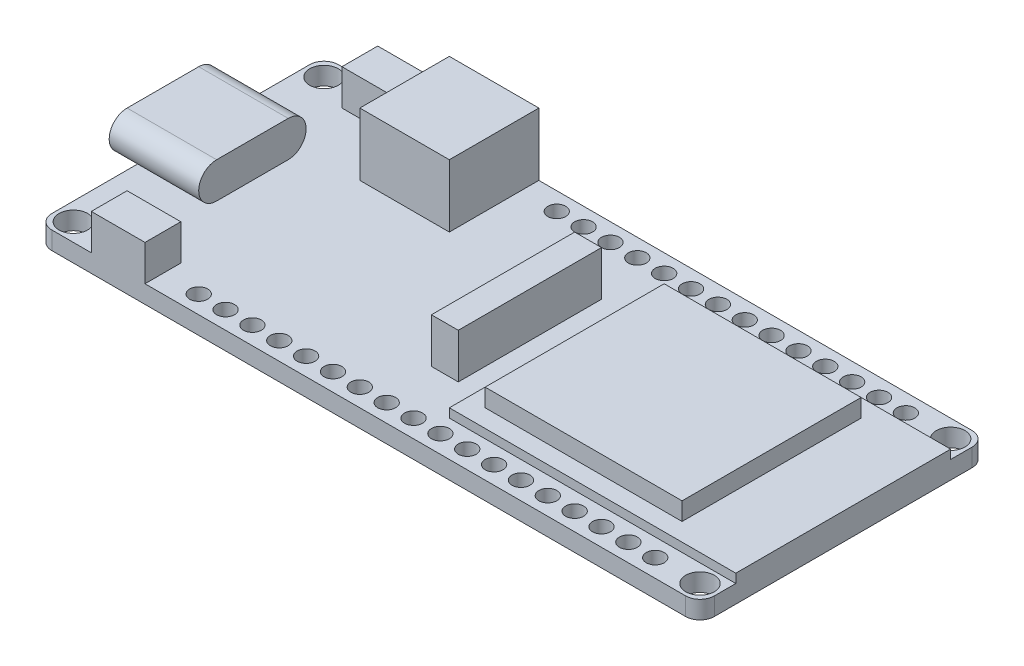
SolidWorks part; units mm, degrees
ref_plane "Front Plane" through (0, 0, 0) normal (0, 0, 1) x (1, 0, 0)
ref_plane "Top Plane" through (0, 0, 0) normal (0, 1, 0) x (1, 0, 0)
ref_plane "Right Plane" through (0, 0, 0) normal (1, 0, 0) x (0, 0, -1)
sketch "Sketch1" plane through (0, 0, 0) normal (0, 1, 0) x (1, 0, 0)
  line L1 (0, 0) -> (60.325, 0)
  line L2 (0, 0) -> (0, 25.4)
  line L3 (0, 25.4) -> (60.325, 25.4)
  line L4 (60.325, 0) -> (60.325, 25.4)
  line L5 (0, 25.4) -> (1.5875, 25.4)
  line L6 (0, 25.4) -> (0, 17.4625)
  line L7 (0, 17.4625) -> (1.5875, 17.4625)
  line L8 (1.5875, 25.4) -> (1.5875, 17.4625)
  line L9 (0, 0) -> (1.5875, 0)
  line L10 (0, 0) -> (0, 7.9375)
  line L11 (0, 7.9375) -> (1.5875, 7.9375)
  line L12 (1.5875, 0) -> (1.5875, 7.9375)
  dimension "D1" = 60.325
  dimension "D2" = 25.4
  dimension "D3" = 7.9375
  dimension "D4" = 1.5875
  dimension "D5" = 1.5875
  dimension "D6" = 7.9375
extrude "Boss-Extrude1" add sketch "Sketch1" along normal blind 1.5875 contours L12 L1 L4 L3 L8 L7 L2 L11
sketch "Sketch2" plane through (0, 1.5875, 0) normal (0, 1, 0) x (1, 0, 0)
  line L1 (0, 17.4625) -> (7.9375, 17.4625)
  line L2 (0, 17.4625) -> (0, 7.9375)
  line L3 (0, 7.9375) -> (7.9375, 7.9375)
  line L4 (7.9375, 17.4625) -> (7.9375, 7.9375)
  dimension "D1" = 9.525
  dimension "D2" = 7.9375
extrude "Boss-Extrude2" add sketch "Sketch2" along normal blind 3.175
sketch "Sketch3" plane through (0, 0, 0) normal (-1, 0, 0) x (0, 0, 1)
  line L0 (-7.9375, 4.7625) -> (-7.9375, 0) construction
  line L1 (-17.4625, 4.7625) -> (-7.9375, 4.7625)
  line L2 (-17.4625, 4.7625) -> (-17.4625, 1.5875)
  line L3 (-17.4625, 1.5875) -> (-7.9375, 1.5875)
  line L4 (-7.9375, 4.7625) -> (-7.9375, 1.5875)
  line L5 (-15.875, 3.175) -> (-9.525, 3.175) construction
  line L6 (-15.875, 4.7625) -> (-9.525, 4.7625)
  line L7 (-15.875, 1.5875) -> (-9.525, 1.5875)
  line L8 (-15.875, 3.175) -> (-9.525, 3.175) construction
  line L9 (-15.875, 3.5719) -> (-9.525, 3.5719)
  line L10 (-15.875, 3.5719) -> (-15.875, 2.7781)
  line L11 (-15.875, 2.7781) -> (-9.525, 2.7781)
  line L12 (-9.525, 3.5719) -> (-9.525, 2.7781)
  line L13 (-15.875, 4.3656) -> (-9.525, 4.3656)
  line L14 (-15.875, 1.9844) -> (-9.525, 1.9844)
  arc A0 (-15.875, 4.7625) -> (-15.875, 1.5875) centre (-15.875, 3.175) ccw
  arc A1 (-9.525, 1.5875) -> (-9.525, 4.7625) centre (-9.525, 3.175) ccw
  arc A2 (-15.875, 4.3656) -> (-15.875, 1.9844) centre (-15.875, 3.175) ccw
  arc A3 (-9.525, 1.9844) -> (-9.525, 4.3656) centre (-9.525, 3.175) ccw
  point P9 (-12.7, 3.175)
  point P16 (-12.7, 3.175)
  point P17 (-17.4625, 3.175)
  point P18 (-7.9375, 3.175)
  line M11 (-7.9375, 0) -> (-7.9375, 4.7625)
  line M12 (-7.9375, 4.7625) -> (-17.4625, 4.7625)
  line M13 (-17.4625, 4.7625) -> (-17.4625, 0)
  dimension "D1" = 3.175
  dimension "D2" = 0.7937
  dimension "D3" = 6.35
  dimension "D4" = 0.3969
  dimension "D5" = 3.175
  dimension "D6" = 0.3969
extrude "Cut-Extrude2" cut sketch "Sketch3" against normal blind 7.9375 contours A0 M12 M13 | A0 L2 L3 | A1 L4 M12 | A1 L3 M11
sketch "Sketch4" plane through (0, 0, 0) normal (-1, 0, 0) x (0, 0, 1)
  line L0 (-15.875, 3.175) -> (-9.525, 3.175) construction
  line L1 (-15.875, 4.3656) -> (-9.525, 4.3656)
  line L2 (-15.875, 1.9844) -> (-9.525, 1.9844)
  line L4 (-15.875, 1.5875) -> (-9.525, 1.5875)
  line L5 (-15.875, 4.7625) -> (-9.525, 4.7625) construction
  line L6 (-15.875, 3.5719) -> (-9.525, 3.5719)
  line L7 (-15.875, 3.5719) -> (-15.875, 2.7781)
  line L8 (-15.875, 2.7781) -> (-9.525, 2.7781)
  line L9 (-9.525, 3.5719) -> (-9.525, 2.7781)
  arc A0 (-15.875, 4.3656) -> (-15.875, 1.9844) centre (-15.875, 3.175) ccw
  arc A1 (-9.525, 1.9844) -> (-9.525, 4.3656) centre (-9.525, 3.175) ccw
  arc A3 (-15.875, 4.7625) -> (-15.875, 1.5875) centre (-15.875, 3.175) ccw construction
  arc A4 (-9.525, 1.5875) -> (-9.525, 4.7625) centre (-9.525, 3.175) ccw construction
  point P2 (-12.7, 3.175)
  dimension "D3" = 6.35
  dimension "D1" = 0.3969
  dimension "D2" = 0.3969
  dimension "D4" = 0.7937
  dimension "D5" = 3.175
extrude "Cut-Extrude3" cut sketch "Sketch4" against normal blind 5.3975 contours L2 A1 L1 A0 L6 L9 L8 L7
sketch "Sketch5" plane through (0, 0, 0) normal (0, -1, 0) x (1, 0, 0)
  line L1 (0, -17.4625) -> (1.5875, -17.4625)
  line L2 (0, -17.4625) -> (0, -7.9375)
  line L3 (0, -7.9375) -> (1.5875, -7.9375)
  line L4 (1.5875, -17.4625) -> (1.5875, -7.9375)
extrude "Cut-Extrude4" cut sketch "Sketch5" against normal blind 1.5875
sketch "Sketch6" plane through (0, 1.5875, 0) normal (0, 1, 0) x (1, 0, 0)
  line L0 (1.5875, 25.4) -> (60.325, 25.4) construction
  line L1 (1.5875, 25.4) -> (1.5875, 15.875) construction
  line L2 (60.325, 0) -> (60.325, 25.4) construction
  line L3 (1.5875, 0) -> (60.325, 0) construction
  line L9 (2.8575, 25.4) -> (59.055, 25.4)
  line L10 (1.5875, 24.13) -> (1.5875, 1.27)
  line L11 (2.8575, 0) -> (59.055, 0)
  line L12 (60.325, 24.13) -> (60.325, 1.27)
  line L13 (1.5875, 25.4) -> (60.325, 25.4)
  line L14 (1.5875, 25.4) -> (1.5875, 0)
  line L15 (1.5875, 0) -> (60.325, 0)
  line L16 (60.325, 25.4) -> (60.325, 0)
  circle A0 centre (3.175, 23.8125) radius 1.27
  circle A1 centre (3.175, 1.5875) radius 1.27
  circle A2 centre (58.7375, 1.5875) radius 1.27
  circle A3 centre (58.7375, 23.8125) radius 1.27
  arc A4 (59.055, 25.4) -> (60.325, 24.13) centre (59.055, 24.13) cw
  arc A5 (59.055, 0) -> (60.325, 1.27) centre (59.055, 1.27) ccw
  arc A6 (2.8575, 0) -> (1.5875, 1.27) centre (2.8575, 1.27) cw
  arc A7 (1.5875, 24.13) -> (2.8575, 25.4) centre (2.8575, 24.13) cw
  point P27 (60.325, 0)
  point P32 (1.5875, 25.4)
  line M18 (1.5875, 9.525) -> (1.5875, 0)
  line M19 (1.5875, 0) -> (60.325, 0)
  line M20 (60.325, 0) -> (60.325, 25.4)
  line M21 (60.325, 25.4) -> (1.5875, 25.4)
  line M22 (1.5875, 25.4) -> (1.5875, 15.875)
  dimension "D6" = 1.27
  dimension "D2" = 1.5875
  dimension "D3" = 1.5875
  dimension "D4" = 1.5875
  dimension "D5" = 1.5875
extrude "Cut-Extrude5" cut sketch "Sketch6" against normal blind 1.5875 contours A7 M22 M21 | A6 M19 M18 | A5 M19 M20 | A4 M21 M20 | A0 | A1 | A2 | A3
sketch "Sketch7" plane through (0, 1.5875, 0) normal (0, 1, 0) x (1, 0, 0)
  line L0 (2.8575, 25.4) -> (59.055, 25.4) construction
  line L1 (6.35, 25.4) -> (11.1125, 25.4)
  line L2 (6.35, 25.4) -> (6.35, 22.225)
  line L3 (6.35, 22.225) -> (11.1125, 22.225)
  line L4 (11.1125, 25.4) -> (11.1125, 22.225)
  line L5 (1.5875, 24.13) -> (1.5875, 15.875) construction
  line L6 (12.7, 25.4) -> (20.6375, 25.4)
  line L7 (12.7, 25.4) -> (12.7, 17.4625)
  line L8 (12.7, 17.4625) -> (20.6375, 17.4625)
  line L9 (20.6375, 25.4) -> (20.6375, 17.4625)
  line L10 (60.325, 1.27) -> (60.325, 24.13) construction
  line L11 (60.325, 22.225) -> (34.925, 22.225)
  line L12 (60.325, 22.225) -> (60.325, 3.175)
  line L13 (60.325, 3.175) -> (34.925, 3.175)
  line L14 (34.925, 22.225) -> (34.925, 3.175)
  line L15 (2.8575, 0) -> (59.055, 0) construction
  line L17 (36.5125, 20.6375) -> (54.1337, 20.6375)
  line L18 (36.5125, 20.6375) -> (36.5125, 4.7625)
  line L19 (36.5125, 4.7625) -> (54.1337, 4.7625)
  line L20 (54.1337, 20.6375) -> (54.1337, 4.7625)
  line L21 (30.1625, 19.05) -> (32.5437, 19.05)
  line L22 (30.1625, 19.05) -> (30.1625, 6.35)
  line L23 (30.1625, 6.35) -> (32.5437, 6.35)
  line L24 (32.5437, 19.05) -> (32.5437, 6.35)
  line L25 (6.35, 0) -> (11.1125, 0)
  line L26 (6.35, 0) -> (6.35, 3.175)
  line L27 (6.35, 3.175) -> (11.1125, 3.175)
  line L28 (11.1125, 0) -> (11.1125, 3.175)
  line M32 (60.325, 1.27) -> (60.325, 24.13)
  line M34 (59.055, 25.4) -> (2.8575, 25.4)
  dimension "D1" = 1.5875
  dimension "D2" = 7.9375
  dimension "D3" = 7.9375
  dimension "D4" = 4.7625
  dimension "D5" = 3.175
  dimension "D6" = 4.7625
  dimension "D7" = 3.175
  dimension "D8" = 3.175
  dimension "D9" = 25.4
  dimension "D10" = 1.5875
  dimension "D11" = 1.5875
  dimension "D12" = 1.5875
  dimension "D13" = 17.6212
  dimension "D14" = 2.3813
  dimension "D15" = 2.3813
  dimension "D16" = 6.35
  dimension "D17" = 6.35
extrude "Boss-Extrude3" add sketch "Sketch7" along normal blind 3.175 contours L20 L17 L18 L19 | L11 L14 L13 L17 L20 L19 L18 M32 | L4 L2 L3 M34 | L26 L25 L28 L27 | L7 L6 L9 L8 | L22 L21 L24 L23
sketch "Sketch10" plane through (0, 4.7625, 0) normal (0, 1, 0) x (1, 0, 0)
  line L0 (12.7, 17.4625) -> (20.6375, 17.4625) construction
  line L1 (12.7, 25.4) -> (20.6375, 25.4)
  line L2 (12.7, 25.4) -> (12.7, 17.4625)
  line L3 (12.7, 17.4625) -> (20.6375, 17.4625)
  line L4 (20.6375, 25.4) -> (20.6375, 17.4625)
extrude "Boss-Extrude4" add sketch "Sketch10" along normal blind 2.3813
sketch "Sketch11" plane through (0, 4.7625, 0) normal (0, 1, 0) x (1, 0, 0)
  line L1 (30.1625, 19.05) -> (32.5437, 19.05)
  line L2 (30.1625, 19.05) -> (30.1625, 6.35)
  line L3 (30.1625, 6.35) -> (32.5437, 6.35)
  line L4 (32.5437, 19.05) -> (32.5437, 6.35)
extrude "Boss-Extrude5" add sketch "Sketch11" along normal blind 0.7937
sketch "Sketch12" plane through (0, 4.7625, 0) normal (0, 1, 0) x (1, 0, 0)
  line L1 (34.925, 22.225) -> (60.325, 22.225)
  line L2 (34.925, 22.225) -> (34.925, 3.175)
  line L3 (34.925, 3.175) -> (60.325, 3.175)
  line L4 (60.325, 22.225) -> (60.325, 3.175)
extrude "Cut-Extrude6" cut sketch "Sketch12" against normal blind 0.7937
sketch "Sketch13" plane through (0, 3.9687, 0) normal (0, 1, 0) x (1, 0, 0)
  line L1 (34.925, 22.225) -> (60.325, 22.225)
  line L2 (34.925, 22.225) -> (34.925, 3.175)
  line L3 (34.925, 3.175) -> (60.325, 3.175)
  line L4 (60.325, 22.225) -> (60.325, 3.175)
  line L5 (36.5125, 20.6375) -> (53.975, 20.6375)
  line L6 (36.5125, 20.6375) -> (36.5125, 4.7625)
  line L7 (36.5125, 4.7625) -> (53.975, 4.7625)
  line L8 (53.975, 20.6375) -> (53.975, 4.7625)
  dimension "D1" = 1.5875
  dimension "D2" = 1.5875
  dimension "D3" = 1.5875
  dimension "D4" = 6.35
extrude "Cut-Extrude7" cut sketch "Sketch13" against normal blind 1.5875 contours L6 L5 L8 L7 | L2 L1 L4 L3
sketch "Sketch14" plane through (0, 1.5875, 0) normal (0, 1, 0) x (1, 0, 0)
  line L1 (60.325, 1.27) -> (60.325, 3.175) construction
  line L2 (60.325, 22.225) -> (60.325, 24.13) construction
  line L3 (20.6375, 25.4) -> (59.055, 25.4) construction
  line L4 (11.1125, 0) -> (59.055, 0) construction
  circle A0 centre (23.8125, 23.8125) radius 0.7937
  circle A1 centre (26.1937, 23.8125) radius 0.7937
  circle A2 centre (28.575, 23.8125) radius 0.7937
  circle A3 centre (30.9562, 23.8125) radius 0.7937
  circle A5 centre (38.1, 23.8125) radius 0.7937
  circle A6 centre (42.8625, 23.8125) radius 0.7937
  circle A7 centre (33.3375, 23.8125) radius 0.7937
  circle A8 centre (35.7187, 23.8125) radius 0.7937
  circle A9 centre (40.4812, 23.8125) radius 0.7937
  circle A10 centre (45.2437, 23.8125) radius 0.7937
  circle A11 centre (47.625, 23.8125) radius 0.7937
  circle A12 centre (50.0062, 23.8125) radius 0.7937
  circle A13 centre (52.3875, 23.8125) radius 0.7937
  circle A14 centre (54.7687, 23.8125) radius 0.7937
  circle A15 centre (14.2875, 1.5875) radius 0.7937
  circle A16 centre (16.6687, 1.5875) radius 0.7937
  circle A17 centre (19.05, 1.5875) radius 0.7937
  circle A18 centre (21.4312, 1.5875) radius 0.7937
  circle A19 centre (23.8125, 1.5875) radius 0.7937
  circle A20 centre (26.1937, 1.5875) radius 0.7937
  circle A21 centre (28.575, 1.5875) radius 0.7937
  circle A22 centre (30.9562, 1.5875) radius 0.7937
  circle A23 centre (33.3375, 1.5875) radius 0.7937
  circle A24 centre (35.7187, 1.5875) radius 0.7937
  circle A25 centre (38.1, 1.5875) radius 0.7937
  circle A26 centre (40.4812, 1.5875) radius 0.7937
  circle A27 centre (42.8625, 1.5875) radius 0.7937
  circle A28 centre (45.2437, 1.5875) radius 0.7937
  circle A29 centre (47.625, 1.5875) radius 0.7937
  circle A30 centre (50.0062, 1.5875) radius 0.7937
  circle A31 centre (52.3875, 1.5875) radius 0.7937
  circle A32 centre (54.7687, 1.5875) radius 0.7937
  dimension "D7" = 1.5875
  dimension "D16" = 1.5875
  dimension "D2" = 2.3813
  dimension "D3" = 2.3813
  dimension "D4" = 2.3813
  dimension "D5" = 2.3813
  dimension "D6" = 2.3813
  dimension "D8" = 2.3813
  dimension "D9" = 2.3813
  dimension "D10" = 2.3813
  dimension "D11" = 2.3813
  dimension "D12" = 2.3813
  dimension "D13" = 2.3813
  dimension "D14" = 2.3813
  dimension "D15" = 2.3813
  dimension "D17" = 2.3813
  dimension "D18" = 2.3813
  dimension "D19" = 2.3813
  dimension "D20" = 2.3813
  dimension "D21" = 2.3813
  dimension "D22" = 2.3813
  dimension "D23" = 2.3813
  dimension "D24" = 2.3813
  dimension "D25" = 2.3813
  dimension "D26" = 2.3813
  dimension "D27" = 2.3813
  dimension "D28" = 2.3813
  dimension "D29" = 2.3813
  dimension "D30" = 2.3813
  dimension "D31" = 2.3813
  dimension "D32" = 2.3813
  dimension "D33" = 2.3813
  dimension "D34" = 5.5562
  dimension "D35" = 5.5562
  dimension "D36" = 1.5875
  dimension "D37" = 1.5875
extrude "Cut-Extrude8" cut sketch "Sketch14" against normal blind 1.5875
